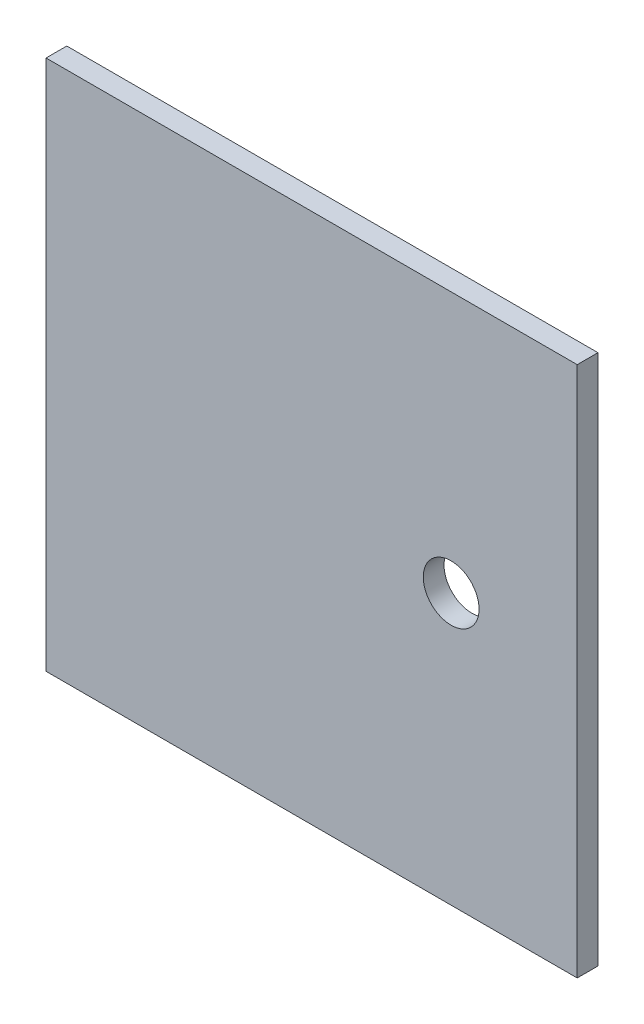
SolidWorks part; units mm, degrees
ref_plane "Front Plane" through (0, 0, 0) normal (0, 0, 1) x (1, 0, 0)
ref_plane "Top Plane" through (0, 0, 0) normal (0, 1, 0) x (1, 0, 0)
ref_plane "Right Plane" through (0, 0, 0) normal (1, 0, 0) x (0, 0, -1)
sketch "Sketch1" plane through (0, 0, 0) normal (0, 0, 1) x (1, 0, 0)
  line L1 (0, 0) -> (80, 0)
  line L2 (0, 0) -> (0, 80)
  line L3 (0, 80) -> (80, 80)
  line L4 (80, 0) -> (80, 80)
  dimension "D1" = 80
  dimension "D2" = 80
extrude "Boss-Extrude1" add sketch "Sketch1" along normal blind 3.125
sketch "Sketch2" plane through (0, 0, 3.125) normal (0, 0, 1) x (1, 0, 0)
  circle A0 centre (61.0147, 40.7152) radius 4.2
extrude "Cut-Extrude1" cut sketch "Sketch2" against normal through all
